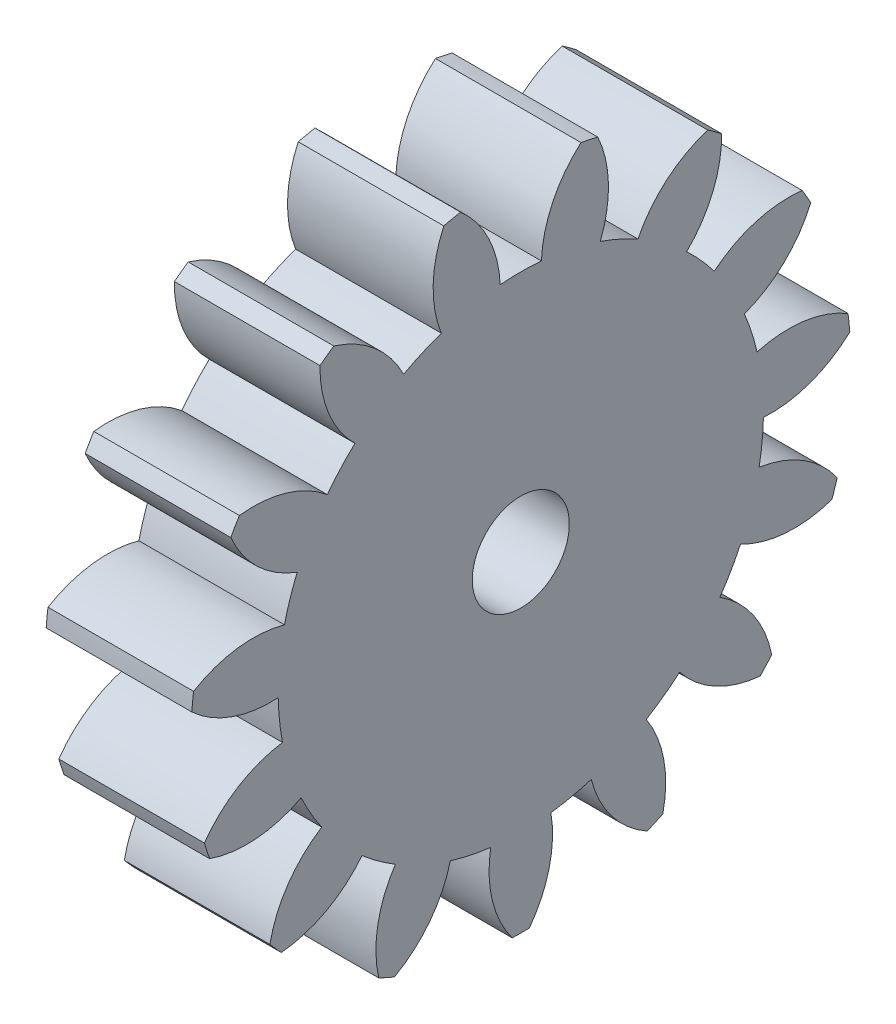
SolidWorks part; units mm, degrees
ref_plane "Plane1" through (0, 0, 0) normal (0, 0, 1) x (1, 0, 0)
ref_plane "Plane2" through (0, 0, 0) normal (0, 1, 0) x (1, 0, 0)
ref_plane "Plane3" through (0, 0, 0) normal (1, 0, 0) x (0, 0, -1)
sketch "HoldingSke" plane through (0, 0, 0) normal (0, 1, 0) x (1, 0, 0)
  line L0 (0, 0) -> (122.6726, -32.87)
  line L1 (-15, 0) -> (100, 0) construction
  line L2 (0, 0) -> (-2.1039, 2.3779)
  line L3 (0, 0) -> (-11.863, 4.5341)
  line L4 (0, 0) -> (8.3417, 2.2352)
  line L5 (0, 0) -> (-47.5972, -17.7524)
  line L6 (0, 0) -> (-15.7917, -10.6547)
  line L7 (-2.1039, 2.3779) -> (8.8308, 51.9871)
  line L8 (-76.2, 54.61) -> (-61.976, 54.61)
  line L9 (-71.009, 38.7566) -> (-53.1078, 45.2721)
  line L10 (-76.2, 71.12) -> (104.1128, 71.12)
  line L11 (0, 0) -> (-19.05, 0)
  line L12 (-76.2, 101.6) -> (-76.0095, 101.6)
  line L13 (24.9733, 27.94) -> (52.9518, 28.4284)
  line L14 (24.9733, 27.94) -> (24.9746, 27.94)
  line L15 (24.9733, 27.94) -> (100.4006, 29.5858)
  circle A0 centre (0, 0) radius 6.35
  circle A1 centre (0, 0) radius 31.7487
  circle A2 centre (0, 0) radius 38.1
  circle A3 centre (0, 0) radius 6.35
  dimension "Hub_dia" = 76.2
  dimension "Bore" = 12.7
  dimension "MBD" = 12.7
  dimension "Pitch" = 127
  dimension "Overall_len" = 50.8
  dimension "Thickness" = 19.05
  dimension "OAL" = 50.8001
  dimension "T_dim" = 14.224
  dimension "Ap" = 20
  dimension "H" = 19.05
  dimension "Pitch_radius" = 180.3128
  dimension "Width" = 19.05
  dimension "Backlash" = 0.1905
  dimension "Addendum_fac" = 1
  dimension "Dedendum_fac" = 1.25
  dimension "Clearance_fac" = 0.25
  dimension "Dedendum_add" = 0.0013
sketch "BasProSke" plane through (0, 0, 0) normal (0, 1, 0) x (1, 0, 0)
  line L0 (-10, 0) -> (60, 0) construction
  line L1 (0, 0) -> (0, 43.18)
  line L2 (0, 0) -> (19.05, 0)
  line L3 (19.05, 0) -> (19.05, 43.18)
  line L4 (19.05, 43.18) -> (0, 43.18)
  dimension "Thickness" = 19.05
revolve "Base-Revolve" add sketch "BasProSke" angle 360 about L0
sketch "TooCutSke" plane through (0, 0, 0) normal (1, 0, 0) x (0, 0, -1)
  line L1 (0, 0) -> (0, 107) construction
  line L2 (0, 0) -> (-4.3156, 37.8548) construction
  line L3 (0, 0) -> (-15.77, 74.1922) construction
  line L4 (-4.3156, 37.8548) -> (-7.885, 37.0961) construction
  arc A0 (2.6969, 31.634) -> (-2.6969, 31.634) centre (0, 0) ccw
  arc A1 (7.904, 42.4763) -> (-7.904, 42.4763) centre (0, 0) ccw
  circle A2 centre (0, 0) radius 38.1 construction
  circle A3 centre (0, 0) radius 35.8023 construction
  arc A4 (-2.6969, 31.634) -> (-7.904, 42.4763) centre (-17.9234, 30.9929) ccw
  arc A5 (7.904, 42.4763) -> (2.6969, 31.634) centre (17.9234, 30.9929) ccw
  dimension "Half_CT" = 3.6492
extrude "ToothCut" cut sketch "TooCutSke" along normal through all
fillet "Breaks" [suppressed] radius 0.1016
fillet "RootFillets" [suppressed] radius 1.2713
pattern_circular "TeethCuts" count 15 every 24 about axis through (-10, 0, 0) along (1, 0, 0) of "ToothCut", "RootFillets", "Breaks"
sketch "HubNeaOneSke" plane through (0, 0, 0) normal (-1, 0, 0) x (0, 0, 1)
  circle A0 centre (0, 0) radius 31.7487
extrude "HubNearOne" [suppressed] add sketch "HubNeaOneSke" along normal blind 31.7501
sketch "HubNeaBotSke" plane through (0, 0, 0) normal (-1, 0, 0) x (0, 0, 1)
  circle A0 centre (0, 0) radius 31.7487
extrude "HubNearBoth" [suppressed] add sketch "HubNeaBotSke" along normal blind 15.875
ref_plane "FarPln" through (19.05, 0, 0) normal (1, 0, 0) x (0, 0, -1)
sketch "HubFarSke" plane through (19.05, 0, 0) normal (1, 0, 0) x (0, 0, -1)
  circle A0 centre (0, 0) radius 31.7487
extrude "HubFar" [suppressed] add sketch "HubFarSke" along normal blind 15.875
sketch "BorSke" plane through (0, 0, 0) normal (1, 0, 0) x (0, 0, -1)
  circle A0 centre (0, 0) radius 6.35
  dimension "Diameter" = 12.7
extrude "Bore" cut sketch "BorSke" along normal mid plane 101.6001
sketch "KeySke" plane through (0, 0, 0) normal (1, 0, 0) x (0, 0, -1)
  line L0 (-1.5875, 0) -> (-1.5875, 7.874)
  line L1 (-1.5875, 7.874) -> (1.5875, 7.874)
  line L2 (1.5875, 7.874) -> (1.5875, 0)
  line L3 (0, 0) -> (0, 34) construction
  line L4 (-1.5875, 0) -> (1.5875, 0)
  dimension "Offset" = 7.874
  dimension "Width" = 3.175
extrude "Keyway" [suppressed] cut sketch "KeySke" along normal mid plane 101.6001
pattern_circular "Keyway2" [suppressed] count 2 every 90 about axis through (-10, 0, 0) along (1, 0, 0)
equation "' \"Pitch@HoldingSke\" = 4"
equation "' \"Num_teeth@HoldingSke\" = 12"
equation "' \"Ap@HoldingSke\" =  20"
equation "' \"Ap@HoldingSke\" = 20"
equation "' \"Width@HoldingSke\" = 0.5"
equation "' \"Hub_dia@HoldingSke\"= 1"
equation "' \"Hub_dia@HoldingSke\" = 1"
equation "' \"Overall_len@HoldingSke\" = 1.0"
equation "' \"Bore@HoldingSke\" = 0.75"
equation "' \"T_dim@HoldingSke\" = 0.85"
equation "' \"Width@KeySke\" = 0.25"
equation "' \"Show_teeth@HoldingSke\" = 13"
equation "' \"Backlash@HoldingSke\" = 0.009"
equation "' \"Addendum_fac@HoldingSke\" = 1.0"
equation "' \"Dedendum_fac@HoldingSke\" = 1.25"
equation "' \"Dedendum_add@HoldingSke\" = 0.00005"
equation "' \"Clearance_fac@HoldingSke\" = 0.25"
equation "' \"Pitch@HoldingSke\" = 0.5"
equation "' \"Num_teeth@HoldingSke\" = 23"
equation "' \"Show_teeth@HoldingSke\" = 23"
equation "' \"Backlash@HoldingSke\" = 0.0375"
equation "\"Overcut_dia@TooCutSke\" = (\"Num_teeth@HoldingSke\" + 2 * \"Addendum_fac@HoldingSke\") / \"Pitch@HoldingSke\" + 0.002"
equation "\"Pitch_dia@TooCutSke\" = \"Num_teeth@HoldingSke\" / \"Pitch@HoldingSke\""
equation "\"Base_dia@TooCutSke\" = \"Num_teeth@HoldingSke\" / \"Pitch@HoldingSke\" * cos((\"Ap@HoldingSke\"  * 3.14159265 / 180))"
equation "\"Root_dia@TooCutSke\" = (\"Num_teeth@HoldingSke\" + 2) / \"Pitch@HoldingSke\" - 2 * (\"Addendum_fac@HoldingSke\" + \"Dedendum_fac@HoldingSke\") / \"Pitch@HoldingSke\" - \"Dedendum_add@HoldingSke\" * 2"
equation "\"Half_ang@TooCutSke\" = 180 / \"Num_teeth@HoldingSke\""
equation "\"Half_CT@TooCutSke\" = \"Num_teeth@HoldingSke\" / \"Pitch@HoldingSke\" * sin((3.14159265 / 2 / \"Num_teeth@HoldingSke\")) / 2 - 7 * \"Backlash@HoldingSke\" / 4"
equation "\"Flank_rad@TooCutSke\" = \"Num_teeth@HoldingSke\" / \"Pitch@HoldingSke\" / 5"
equation "\"Radius@RootFillets\" = \"Clearance_fac@HoldingSke\" / \"Pitch@HoldingSke\" + \"Dedendum_add@HoldingSke\""
equation "\"Break_rad@Breaks\" = 0.02 / \"Pitch@HoldingSke\""
equation "\"Thickness@HoldingSke\" = \"Width@HoldingSke\""
equation "\"OAL@HoldingSke\" = \"Thickness@HoldingSke\""
equation "\"MHD@HoldingSke\" = (\"Num_teeth@HoldingSke\" + 2) / \"Pitch@HoldingSke\" - 2 * (\"Addendum_fac@HoldingSke\" + \"Dedendum_fac@HoldingSke\")  / \"Pitch@HoldingSke\" - \"Dedendum_add@HoldingSke\" * 2"
equation "\"MBD@HoldingSke\" = (\"Num_teeth@HoldingSke\" + 2) / \"Pitch@HoldingSke\" - 2 * (\"Addendum_fac@HoldingSke\" + \"Dedendum_fac@HoldingSke\")  / \"Pitch@HoldingSke\" - \"Dedendum_add@HoldingSke\" * 2 - 0.002"
equation "\"MHD@HoldingSke\" = ((sgn( \"MHD@HoldingSke\" - \"Hub_dia@HoldingSke\" )-1)*( \"MHD@HoldingSke\" - \"Hub_dia@HoldingSke\" ))/-2+ \"Hub_dia@HoldingSke\""
equation "\"MBD@HoldingSke\" = ((sgn( \"MBD@HoldingSke\" - \"Bore@HoldingSke\" )-1)*( \"MBD@HoldingSke\" - \"Bore@HoldingSke\" ))/-2+ \"Bore@HoldingSke\""
equation "\"OAL@HoldingSke\" = ((sgn( \"OAL@HoldingSke\" - \"Overall_len@HoldingSke\" )+1)*( \"OAL@HoldingSke\" - \"Overall_len@HoldingSke\" ))/2 + \"Overall_len@HoldingSke\" + 0.000002"
equation "\"Num_teeth@TeethCuts\" = int( \"Show_teeth@HoldingSke\" ) + 1"
equation "\"Num_teeth@TeethCuts\" = ((sgn( \"Num_teeth@TeethCuts\" - \"Num_teeth@HoldingSke\" )-1)*( \"Num_teeth@TeethCuts\" - \"Num_teeth@HoldingSke\" ))/-2+ \"Num_teeth@HoldingSke\""
equation "\"Num_teeth@TeethCuts\" = ((sgn( \"Num_teeth@TeethCuts\" - 2.0)+1)*( \"Num_teeth@TeethCuts\" - 2.0))/2 +2.0"
equation "\"Angle@TeethCuts\" = 360.0 / \"Num_teeth@HoldingSke\""
equation "\"Diameter@BasProSke\" = (\"Num_teeth@HoldingSke\" + 2 * \"Addendum_fac@HoldingSke\") / \"Pitch@HoldingSke\""
equation "\"Thickness@BasProSke\"  = \"Thickness@HoldingSke\""
equation "' \"Fillet_rad@BasProSke\" =  \"Thickness@HoldingSke\" * 0.05"
equation "' \"Fillet_rad@BasProSke\" = \"Thickness@HoldingSke\" * 0.05"
equation "\"MHD@HoldingSke\" = ((sgn( \"MHD@HoldingSke\" - \"Root_dia@TooCutSke\" )-1)*( \"MHD@HoldingSke\" - \"Root_dia@TooCutSke\" ))/-2+ \"Root_dia@TooCutSke\""
equation "\"Diameter@HubNeaOneSke\" = \"MHD@HoldingSke\""
equation "\"Length@HubNearOne\" = \"OAL@HoldingSke\" - \"Thickness@BasProSke\""
equation "\"Diameter@HubNeaBotSke\" = \"MHD@HoldingSke\""
equation "\"Length@HubNearBoth\" = ( \"OAL@HoldingSke\" - \"Thickness@BasProSke\" ) / 2.0"
equation "\"Thickness@FarPln\" = \"Thickness@BasProSke\""
equation "\"Diameter@HubFarSke\" = \"MHD@HoldingSke\""
equation "\"Length@HubFar\" = ( \"OAL@HoldingSke\" - \"Thickness@BasProSke\" ) / 2.0"
equation "\"Diameter@BorSke\" = \"MBD@HoldingSke\""
equation "\"D1@Bore\" = \"OAL@HoldingSke\" * 2.0"
equation "\"D1@Keyway\" = \"OAL@HoldingSke\" * 2.0"
equation "\"Offset@KeySke\" = \"T_dim@HoldingSke\" - \"MBD@HoldingSke\" / 2.0"
